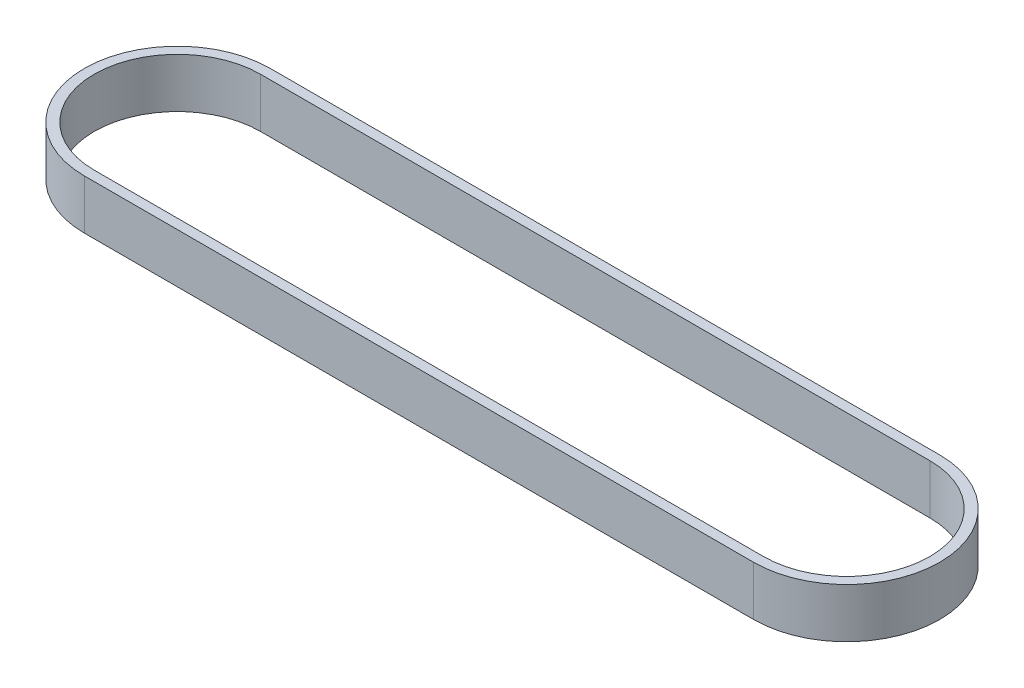
SolidWorks part; units mm, degrees
ref_plane "前视基准面" through (0, 0, 0) normal (0, 0, 1) x (1, 0, 0)
ref_plane "上视基准面" through (0, 0, 0) normal (0, 1, 0) x (1, 0, 0)
ref_plane "右视基准面" through (0, 0, 0) normal (1, 0, 0) x (0, 0, -1)
sketch "草图1" plane through (0, 0, 0) normal (0, 1, 0) x (1, 0, 0)
  line L0 (0, 0) -> (135, 0) construction
  line L1 (0, 17.76) -> (135, 17.76)
  line L2 (0, -17.76) -> (135, -17.76)
  arc A0 (0, 17.76) -> (0, -17.76) centre (0, 0) ccw
  arc A1 (135, -17.76) -> (135, 17.76) centre (135, 0) ccw
  dimension "D2" = 35.52
  dimension "D3" = 35.52
  dimension "D1" = 135
extrude "拉伸-薄壁1" add sketch "草图1" along normal blind 10 thin thin type mid plane wall 2
